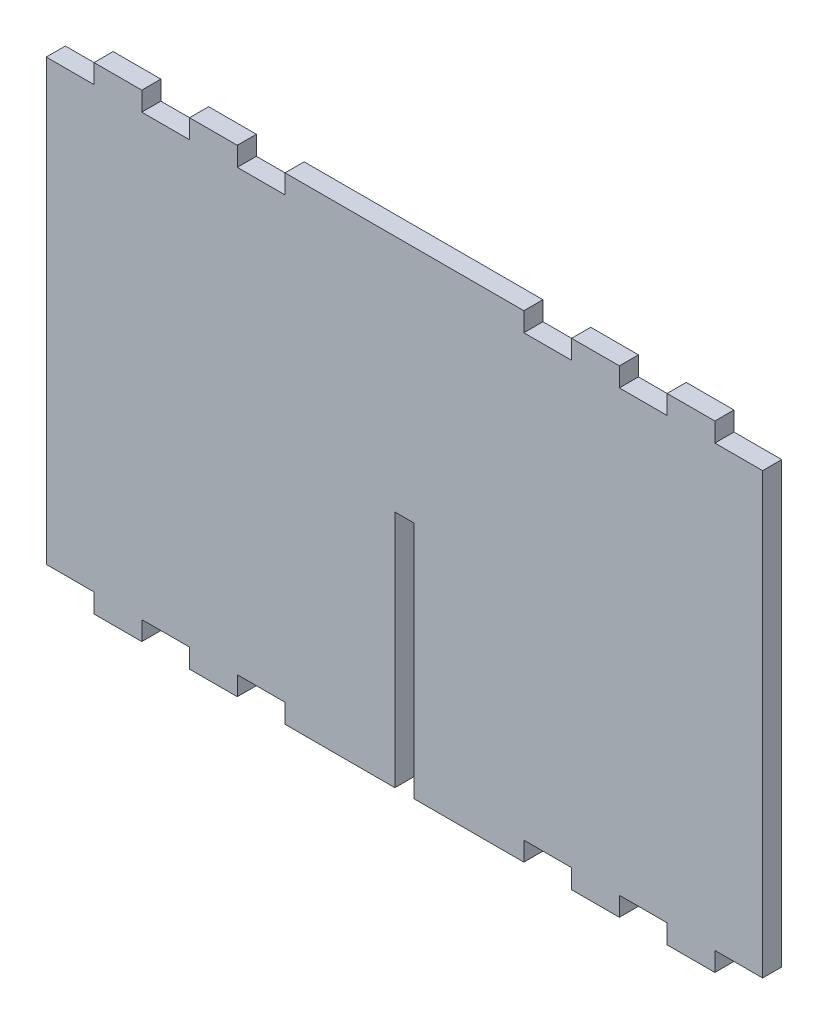
SolidWorks part; units mm, degrees
ref_plane "Front Plane" through (0, 0, 0) normal (0, 0, 1) x (1, 0, 0)
ref_plane "Top Plane" through (0, 0, 0) normal (0, 1, 0) x (1, 0, 0)
ref_plane "Right Plane" through (0, 0, 0) normal (1, 0, 0) x (0, 0, -1)
sketch "Sketch1" plane through (0, 0, 0) normal (0, 0, 1) x (1, 0, 0)
  line L0 (-75, -50) -> (75, -50)
  line L1 (75, -50) -> (75, 50)
  line L2 (75, 50) -> (-75, 50)
  line L3 (-75, 50) -> (-75, -50)
  line L4 (-75, -50) -> (75, 50) construction
  line L5 (-75, 50) -> (75, -50) construction
  point P2 (0, 0)
  dimension "D1" = 150
  dimension "D2" = 100
extrude "Boss-Extrude1" add sketch "Sketch1" along normal blind 4
sketch "Sketch3" plane through (0, 0, 0) normal (0, 0, 1) x (1, 0, 0)
  line L0 (0, 67.8019) -> (0, -57.0444) construction
  line L1 (-55, 46) -> (-45, 46)
  line L2 (-35, 50) -> (-25, 50)
  line L3 (-35, 50) -> (-35, 46)
  line L4 (-35, 46) -> (-25, 46)
  line L5 (75, 50) -> (-75, 50) construction
  line L6 (-282.6394, 0) -> (97.1893, 0) construction
  line L7 (-75, 50) -> (-75, -50) construction
  line L8 (-25, 50) -> (-25, 46)
  line L9 (-45, 50) -> (-45, 46)
  line L10 (-55, 50) -> (-45, 50)
  line L11 (-55, 50) -> (-55, 46)
  line L12 (-75, 46) -> (-65, 46)
  line L13 (-65, 50) -> (-65, 46)
  line L14 (-75, 50) -> (-65, 50)
  line L15 (-75, 50) -> (-75, 46)
  line L16 (75, 50) -> (75, 46)
  line L17 (75, 50) -> (65, 50)
  line L18 (65, 50) -> (65, 46)
  line L19 (75, 46) -> (65, 46)
  line L21 (55, 50) -> (55, 46)
  line L22 (55, 50) -> (45, 50)
  line L23 (45, 50) -> (45, 46)
  line L24 (25, 50) -> (25, 46)
  line L25 (35, 46) -> (25, 46)
  line L26 (35, 50) -> (35, 46)
  line L27 (35, 50) -> (25, 50)
  line L28 (55, 46) -> (45, 46)
  line L29 (55, -46) -> (45, -46)
  line L30 (35, -50) -> (25, -50)
  line L31 (35, -50) -> (35, -46)
  line L32 (35, -46) -> (25, -46)
  line L33 (25, -50) -> (25, -46)
  line L34 (45, -50) -> (45, -46)
  line L35 (55, -50) -> (45, -50)
  line L36 (55, -50) -> (55, -46)
  line L37 (75, -46) -> (65, -46)
  line L38 (65, -50) -> (65, -46)
  line L39 (75, -50) -> (65, -50)
  line L40 (75, -50) -> (75, -46)
  line L41 (-75, -50) -> (-75, -46)
  line L42 (-75, -50) -> (-65, -50)
  line L43 (-65, -50) -> (-65, -46)
  line L44 (-75, -46) -> (-65, -46)
  line L45 (-55, -50) -> (-55, -46)
  line L46 (-55, -50) -> (-45, -50)
  line L47 (-45, -50) -> (-45, -46)
  line L48 (-25, -50) -> (-25, -46)
  line L49 (-35, -46) -> (-25, -46)
  line L50 (-35, -50) -> (-35, -46)
  line L51 (-35, -50) -> (-25, -50)
  line L52 (-55, -46) -> (-45, -46)
  line L53 (-75, -50) -> (75, -50) construction
  line L54 (2, -50) -> (-2, -50)
  line L55 (2, -50) -> (2, 0)
  line L56 (2, 0) -> (-2, 0)
  line L57 (-2, -50) -> (-2, 0)
  point P9 (0, 50)
  point P34 (-75, 0)
  point P64 (0, 0)
  dimension "D1" = 10
  dimension "D2" = 4
  dimension "D3" = 25
  dimension "D4" = 3
extrude "Cut-Extrude2" cut sketch "Sketch3" along direction (0, 0, 1) on the side against the normal through all from surface at 4 starting at face at (0, 0, 4)
